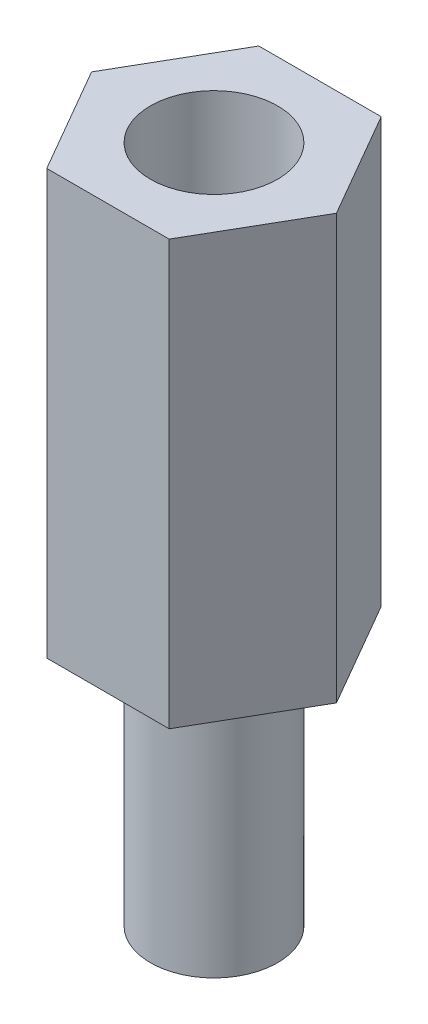
SolidWorks part; units mm, degrees
material "Latón"
ref_plane "Alzado" through (0, 0, 0) normal (0, 0, 1) x (1, 0, 0)
ref_plane "Planta" through (0, 0, 0) normal (0, 1, 0) x (1, 0, 0)
ref_plane "Vista lateral" through (0, 0, 0) normal (1, 0, 0) x (0, 0, -1)
sketch "Croquis1" plane through (0, 0, 0) normal (0, 1, 0) x (1, 0, 0)
  line L1 (1.4434, -2.5) -> (2.8868, 0)
  line L2 (2.8868, 0) -> (1.4434, 2.5)
  line L3 (1.4434, 2.5) -> (-1.4434, 2.5)
  line L4 (-1.4434, 2.5) -> (-2.8868, 0)
  line L5 (-2.8868, 0) -> (-1.4434, -2.5)
  line L6 (-1.4434, -2.5) -> (1.4434, -2.5)
  circle A0 centre (0, 0) radius 2.5 construction
  circle A1 centre (0, 0) radius 1.5
  dimension "D2" = 3
  dimension "D1" = 5
extrude "Saliente-Extruir1" add sketch "Croquis1" along normal blind 10
sketch "Croquis2" plane through (0, 0, 0) normal (0, -1, 0) x (1, 0, 0)
  circle A0 centre (0, 0) radius 1.5 construction
  circle A1 centre (0, 0) radius 1.5
extrude "Saliente-Extruir2" add sketch "Croquis2" along normal blind 6 separate body
